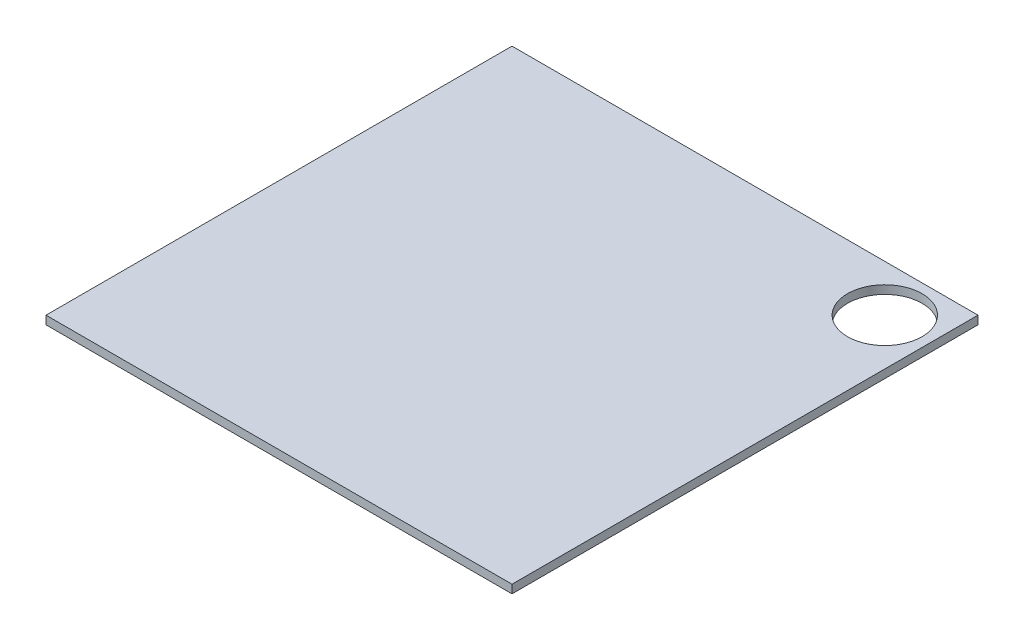
SolidWorks part; units mm, degrees
ref_plane "前视基准面" through (0, 0, 0) normal (0, 0, 1) x (1, 0, 0)
ref_plane "上视基准面" through (0, 0, 0) normal (0, 1, 0) x (1, 0, 0)
ref_plane "右视基准面" through (0, 0, 0) normal (1, 0, 0) x (0, 0, -1)
sketch "草图1" plane through (0, 0, 0) normal (0, 1, 0) x (1, 0, 0)
  line L1 (0, 0) -> (100, 0)
  line L2 (0, 0) -> (0, 100)
  line L3 (0, 100) -> (100, 100)
  line L4 (100, 0) -> (100, 100)
  dimension "D1" = 100
  dimension "D2" = 100
extrude "凸台-拉伸1" add sketch "草图1" along normal blind 1.8
sketch "草图2" plane through (0, 1.8, 0) normal (0, 1, 0) x (1, 0, 0)
  line L0 (100, 0) -> (100, 100) construction
  line L1 (100, 100) -> (0, 100) construction
  circle A0 centre (90, 90) radius 8
  dimension "D1" = 16
  dimension "D2" = 10
  dimension "D3" = 10
extrude "切除-拉伸1" cut sketch "草图2" against normal through all
